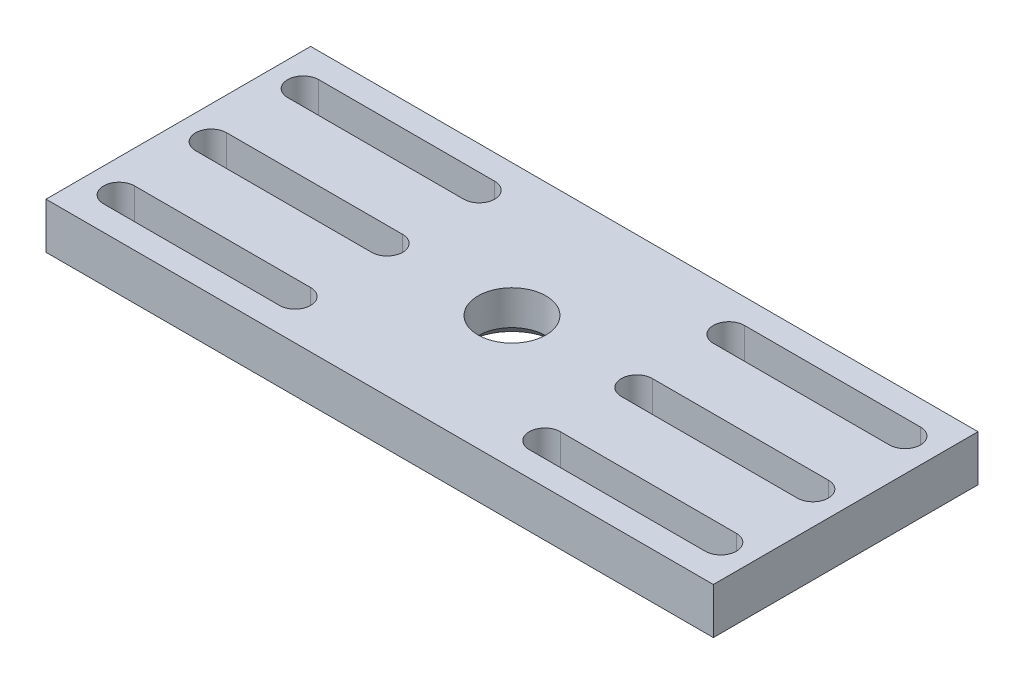
SolidWorks part; units mm, degrees
ref_plane "Front Plane" through (0, 0, 0) normal (0, 0, 1) x (1, 0, 0)
ref_plane "Top Plane" through (0, 0, 0) normal (0, 1, 0) x (1, 0, 0)
ref_plane "Right Plane" through (0, 0, 0) normal (1, 0, 0) x (0, 0, -1)
sketch "Sketch1" plane through (0, 0, 0) normal (0, 1, 0) x (1, 0, 0)
  line L1 (-145, -57.5) -> (145, -57.5)
  line L2 (-145, -57.5) -> (-145, 57.5)
  line L3 (-145, 57.5) -> (145, 57.5)
  line L4 (145, -57.5) -> (145, 57.5)
  line L5 (-145, -57.5) -> (145, 57.5) construction
  line L6 (-145, 57.5) -> (145, -57.5) construction
  point P0 (0, 0)
  dimension "D1" = 290
  dimension "D2" = 115
extrude "Boss-Extrude1" add sketch "Sketch1" along normal blind 20
sketch "Sketch2" plane through (0, 20, 0) normal (0, 1, 0) x (1, 0, 0)
  line L0 (-130.75, 0) -> (-54.25, 0) construction
  line L1 (-130.75, 6.75) -> (-54.25, 6.75)
  line L2 (-130.75, -6.75) -> (-54.25, -6.75)
  line L3 (-130.75, 40) -> (-54.25, 40) construction
  line L4 (-130.75, 46.75) -> (-54.25, 46.75)
  line L5 (-130.75, 33.25) -> (-54.25, 33.25)
  line L6 (-130.75, -40) -> (-54.25, -40) construction
  line L7 (-130.75, -33.25) -> (-54.25, -33.25)
  line L8 (-130.75, -46.75) -> (-54.25, -46.75)
  line L9 (54.25, 0) -> (130.75, 0) construction
  line L10 (54.25, 6.75) -> (130.75, 6.75)
  line L11 (54.25, -6.75) -> (130.75, -6.75)
  line L12 (54.25, -40) -> (130.75, -40) construction
  line L13 (54.25, -33.25) -> (130.75, -33.25)
  line L14 (54.25, -46.75) -> (130.75, -46.75)
  line L15 (54.25, 40) -> (130.75, 40) construction
  line L16 (54.25, 46.75) -> (130.75, 46.75)
  line L17 (54.25, 33.25) -> (130.75, 33.25)
  line L18 (-145, 57.5) -> (-145, -57.5) construction
  line L19 (145, -57.5) -> (145, 57.5) construction
  line L20 (145, 57.5) -> (-145, 57.5) construction
  line L21 (-145, -57.5) -> (145, -57.5) construction
  arc A1 (-130.75, 6.75) -> (-130.75, -6.75) centre (-130.75, 0) ccw
  arc A2 (-54.25, -6.75) -> (-54.25, 6.75) centre (-54.25, 0) ccw
  arc A3 (-130.75, 46.75) -> (-130.75, 33.25) centre (-130.75, 40) ccw
  arc A4 (-54.25, 33.25) -> (-54.25, 46.75) centre (-54.25, 40) ccw
  arc A5 (-130.75, -33.25) -> (-130.75, -46.75) centre (-130.75, -40) ccw
  arc A6 (-54.25, -46.75) -> (-54.25, -33.25) centre (-54.25, -40) ccw
  arc A7 (54.25, 6.75) -> (54.25, -6.75) centre (54.25, 0) ccw
  arc A8 (130.75, -6.75) -> (130.75, 6.75) centre (130.75, 0) ccw
  arc A9 (54.25, -33.25) -> (54.25, -46.75) centre (54.25, -40) ccw
  arc A10 (130.75, -46.75) -> (130.75, -33.25) centre (130.75, -40) ccw
  arc A11 (54.25, 46.75) -> (54.25, 33.25) centre (54.25, 40) ccw
  arc A12 (130.75, 33.25) -> (130.75, 46.75) centre (130.75, 40) ccw
  circle A13 centre (0, 0) radius 14.75
  point P3 (-92.5, 0)
  point P10 (-92.5, 40)
  point P17 (-92.5, -40)
  point P24 (92.5, 0)
  point P31 (92.5, -40)
  point P38 (92.5, 40)
  point P48 (-137.5, 40)
  point P51 (137.5, 40)
  dimension "D2" = 13.5
  dimension "D16" = 29.5
  dimension "D7" = 7.5
  dimension "D8" = 52.5
  dimension "D9" = 7.5
  dimension "D10" = 52.5
  dimension "D11" = 185
  dimension "D12" = 17.5
  dimension "D13" = 17.5
  dimension "D14" = 40
  dimension "D15" = 40
extrude "Cut-Extrude1" cut sketch "Sketch2" against normal blind 20
chamfer "Chamfer1" distance 5 angle 45 1 edges at (0, 0, 14.75)
